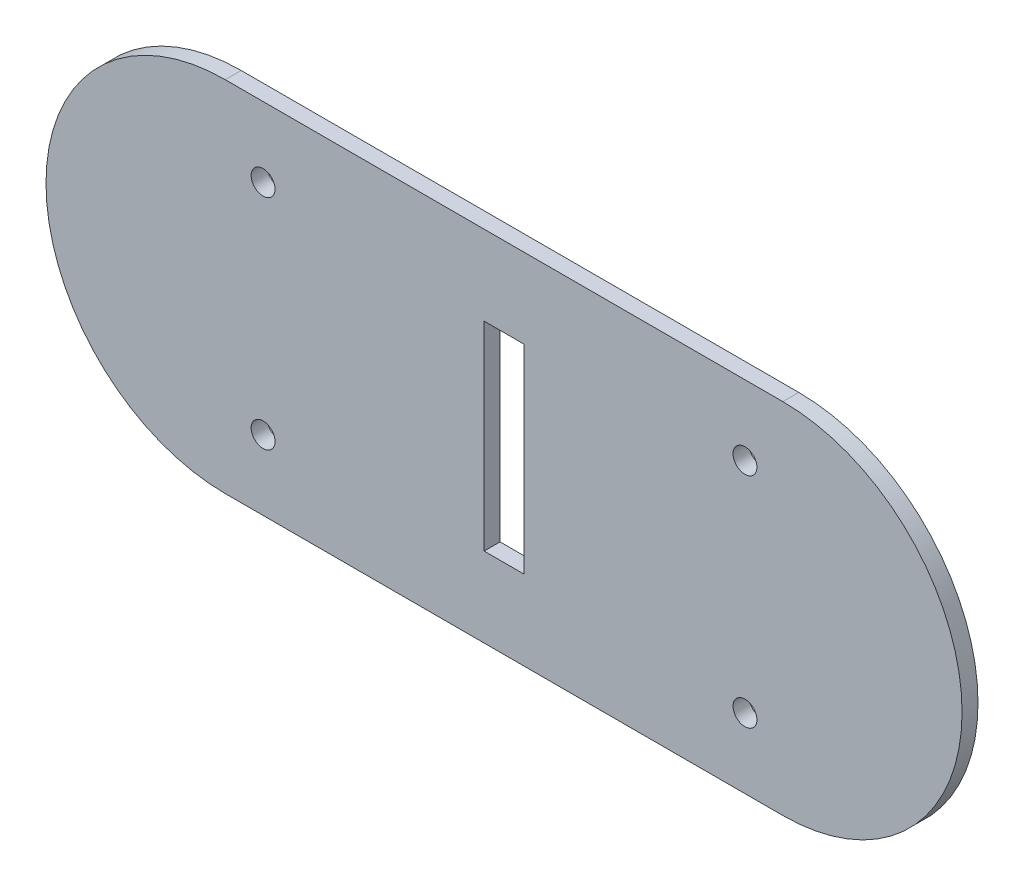
SolidWorks part; units mm, degrees
material "7075-T6 (SN)"
ref_plane "Płaszczyzna XY" through (0, 0, 0) normal (0, 0, 1) x (1, 0, 0)
ref_plane "Płaszczyzna XZ" through (0, 0, 0) normal (0, 1, 0) x (1, 0, 0)
ref_plane "Płaszczyzna YZ" through (0, 0, 0) normal (1, 0, 0) x (0, 0, -1)
sketch "Szkic1" plane through (0, 0, 188.4754) normal (0, 0, 1) x (1, 0, 0)
  line L0 (90.1646, 212.0576) -> (20.1646, 212.0576) construction
  line L1 (90.1646, 189.5576) -> (20.1646, 189.5576)
  line L2 (90.1646, 234.5576) -> (20.1646, 234.5576)
  arc A0 (90.1646, 189.5576) -> (90.1646, 234.5576) centre (90.1646, 212.0576) ccw
  arc A1 (20.1646, 234.5576) -> (20.1646, 189.5576) centre (20.1646, 212.0576) ccw
  point P2 (55.1646, 212.0576)
  dimension "D1" = 70
extrude "Dodanie-wyciągnięcie1" add sketch "Szkic1" along normal blind 2
sketch "Szkic2" plane through (0, 0, 190.4754) normal (0, 0, 1) x (1, 0, 0)
  line L0 (112.6646, 212.0576) -> (-5.1358, 212.0576) construction
  line L1 (55.1646, 234.5576) -> (55.1646, 189.5576) construction
  line L3 (90.1646, 234.5576) -> (20.1646, 234.5576) construction
  line L4 (20.1646, 189.5576) -> (90.1646, 189.5576) construction
  circle A0 centre (85.4115, 225.7773) radius 1.5
  arc A1 (90.1646, 189.5576) -> (90.1646, 234.5576) centre (90.1646, 212.0576) ccw construction
  circle A2 centre (24.9177, 225.7773) radius 1.5
  circle A3 centre (24.9177, 198.3378) radius 1.5
  circle A4 centre (85.4115, 198.3378) radius 1.5
  dimension "D1" = 3
extrude "Wytnij-wyciągnięcie1" cut sketch "Szkic2" against normal blind 2
sketch "Szkic4" plane through (0, 0, 190.4754) normal (0, 0, 1) x (1, 0, 0)
  line L0 (55.1646, 234.5576) -> (55.1646, 189.5576) construction
  line L1 (52.6646, 224.5576) -> (57.6646, 224.5576)
  line L2 (52.6646, 224.5576) -> (52.6646, 199.5576)
  line L3 (52.6646, 199.5576) -> (57.6646, 199.5576)
  line L4 (57.6646, 224.5576) -> (57.6646, 199.5576)
  line L5 (90.1646, 234.5576) -> (20.1646, 234.5576) construction
  line L6 (20.1646, 189.5576) -> (90.1646, 189.5576) construction
  line L7 (-2.3354, 212.0576) -> (115.2667, 212.0576) construction
  arc A0 (20.1646, 234.5576) -> (20.1646, 189.5576) centre (20.1646, 212.0576) ccw construction
  dimension "D1" = 5
  dimension "D2" = 25
extrude "Wytnij-wyciągnięcie2" cut sketch "Szkic4" against normal blind 10
